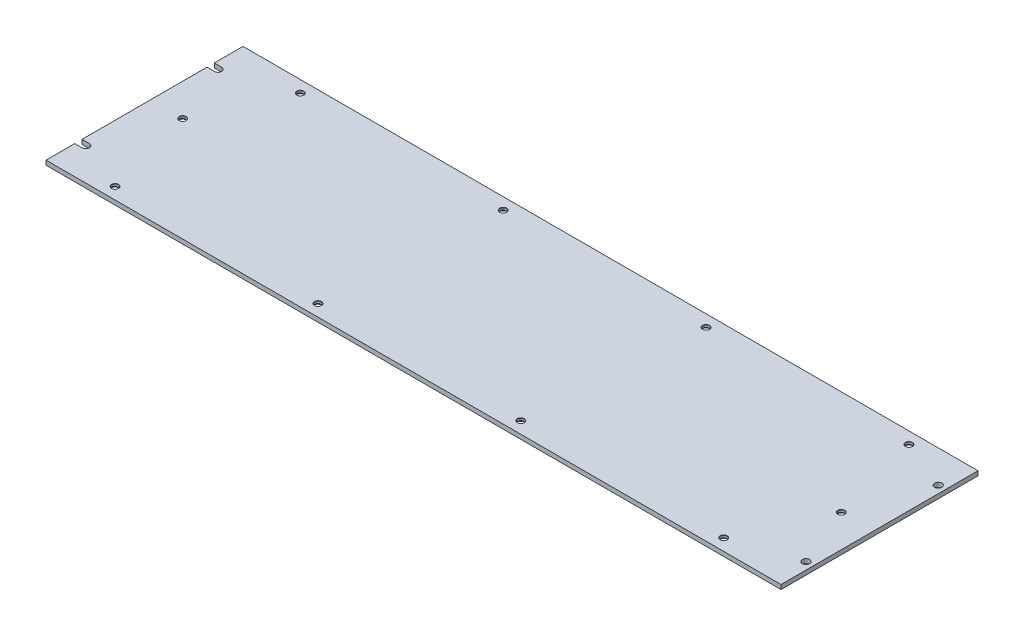
SolidWorks part; units mm, degrees
ref_plane "Спереди" through (0, 0, 0) normal (0, 0, 1) x (1, 0, 0)
ref_plane "Сверху" through (0, 0, 0) normal (0, 1, 0) x (1, 0, 0)
ref_plane "Справа" through (0, 0, 0) normal (1, 0, 0) x (0, 0, -1)
sketch "Эскиз2" plane through (0, 0, 0) normal (0, 1, 0) x (1, 0, 0)
  line L1 (0, 0) -> (500, 0)
  line L2 (0, 0) -> (0, 134)
  line L3 (0, 134) -> (500, 134)
  line L4 (500, 0) -> (500, 134)
  dimension "D1" = 500
  dimension "D2" = 134
extrude "Бобышка-Вытянуть1" add sketch "Эскиз2" along normal blind 3
sketch "Эскиз3" plane through (0, 3, 0) normal (0, 1, 0) x (1, 0, 0)
  line L0 (5, 114.5) -> (0, 114.5)
  line L2 (0, 134) -> (0, 0) construction
  line L3 (5, 109.5) -> (0, 109.5)
  line L4 (5, 24.5) -> (0, 24.5)
  line L5 (5, 19.5) -> (0, 19.5)
  line L6 (500, 0) -> (500, 134) construction
  line L7 (500, 134) -> (0, 134) construction
  circle A0 centre (495, 22) radius 2.5
  circle A1 centre (495, 112) radius 2.5
  arc A2 (5, 114.5) -> (5, 109.5) centre (5, 112) cw
  arc A3 (5, 24.5) -> (5, 19.5) centre (5, 22) cw
  line M1 (0, 134) -> (0, 0)
  dimension "D1" = 5
  dimension "D3" = 5
  dimension "D4" = 90
  dimension "D2" = 490
  dimension "D5" = 22
extrude "Вырез-Вытянуть1" cut sketch "Эскиз3" against normal through all contours A2 L0 L3 M1 | A3 L4 L5 M1 | A0 | A1
hole_wizard "Зенковка для винта с потайной головкой M41" positions "Эскиз5" profile "Эскиз4" countersink size "M4" standard "DIN" end condition through all
sketch "Эскиз5" plane through (0, 0, 0) normal (0, -1, 0) x (1, 0, 0)
  line L0 (0, -19.5) -> (0, 0) construction
  line L1 (0, 0) -> (500, 0) construction
  point P1 (177, -8)
  point P4 (39, -8)
  point P7 (22, -71)
  point P10 (47, -126)
  point P13 (185, -126)
  point P16 (323, -126)
  point P19 (461, -126)
  point P22 (478, -63)
  point P25 (453, -8)
  point P28 (315, -8)
  dimension "D1" = 138
  dimension "D2" = 138
  dimension "D3" = 138
  dimension "D4" = 138
  dimension "D5" = 138
  dimension "D6" = 138
  dimension "D7" = 17
  dimension "D8" = 8
  dimension "D9" = 63
  dimension "D10" = 118
  dimension "D11" = 63
  dimension "D12" = 39
  dimension "D13" = 8
  dimension "D14" = 17
sketch "Эскиз4" plane through (177, 0, -8) normal (1, 0, 0) x (0, 0, -1)
  line L0 (0, 0) -> (0, 3)
  line L1 (0, 3) -> (2.4, 3)
  line L2 (2.25, 2.85) -> (2.25, 1.45)
  line L3 (2.25, 1.45) -> (3.7, 0)
  line L5 (3.7, 0) -> (0, 0)
  line L6 (-2.25, 1.45) -> (-3.7, 0) construction
  line L7 (2.4, 3) -> (2.25, 2.85)
  line L8 (-2.4, 3) -> (-2.25, 2.85) construction
  line L11 (0, -6.35) -> (0, 107.95) construction
  dimension "Диаметр сквозного отверстия" = 4.5
  dimension "Глубина сквозного отверстия" = 3
  dimension "Диаметр передней зенковки" = 7.4
  dimension "Угол передней зенковки" = 90
  dimension "Диаметр задней зенковки" = 4.8
  dimension "Угол задней зенковки" = 90
